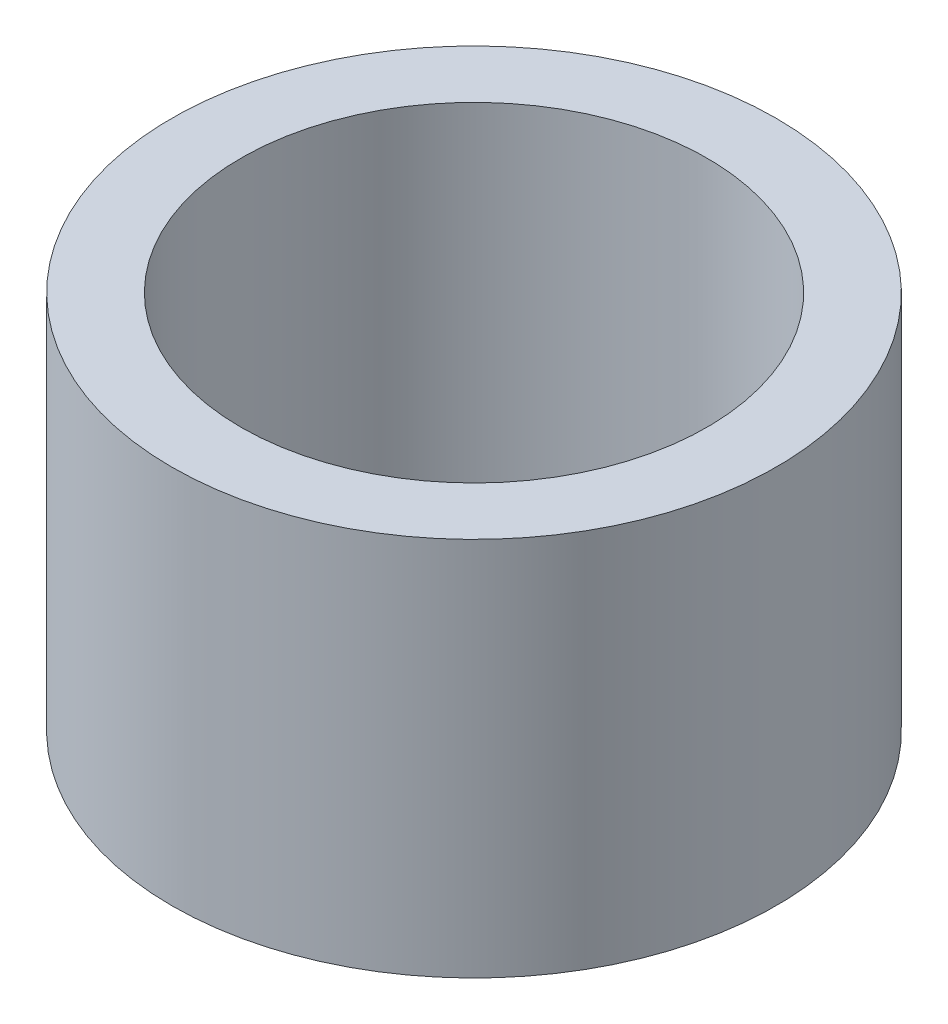
SolidWorks part; units mm, degrees
ref_plane "Front Plane" through (0, 0, 0) normal (0, 0, 1) x (1, 0, 0)
ref_plane "Top Plane" through (0, 0, 0) normal (0, 1, 0) x (1, 0, 0)
ref_plane "Right Plane" through (0, 0, 0) normal (1, 0, 0) x (0, 0, -1)
sketch "Sketch1" plane through (0, 0, 0) normal (0, 1, 0) x (1, 0, 0)
  circle A0 centre (0, 0) radius 3.375
  circle A1 centre (0, 0) radius 4.375
  dimension "D1" = 6.75
  dimension "D2" = 1
extrude "Boss-Extrude1" add sketch "Sketch1" along normal blind 5.5
